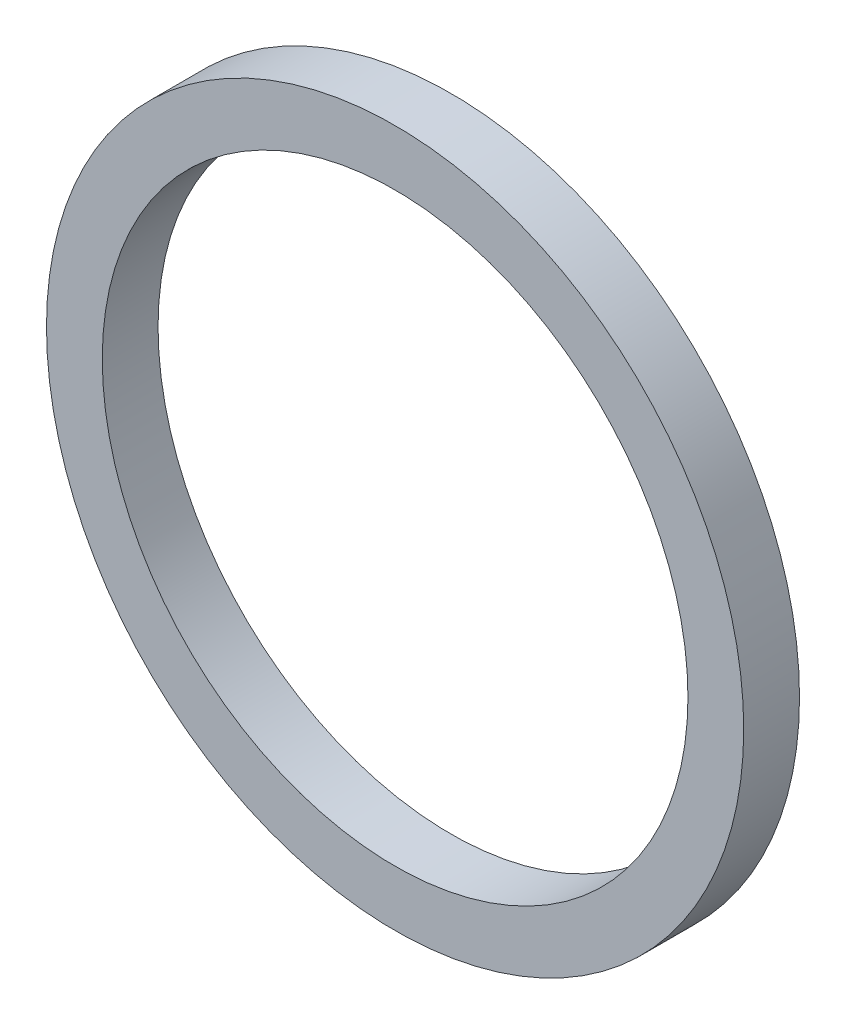
SolidWorks part; units mm, degrees
ref_plane "Front Plane" through (0, 0, 0) normal (0, 0, 1) x (1, 0, 0)
ref_plane "Top Plane" through (0, 0, 0) normal (0, 1, 0) x (1, 0, 0)
ref_plane "Right Plane" through (0, 0, 0) normal (1, 0, 0) x (0, 0, -1)
sketch "Sketch1" plane through (0, 0, 0) normal (0, 0, 1) x (1, 0, 0)
  circle A0 centre (0, 0) radius 18.75
  circle A2 centre (0, 0) radius 15.75
  dimension "D1" = 37.5
  dimension "D2" = 3
extrude "Boss-Extrude1" add sketch "Sketch1" along normal blind 3 contours A2
